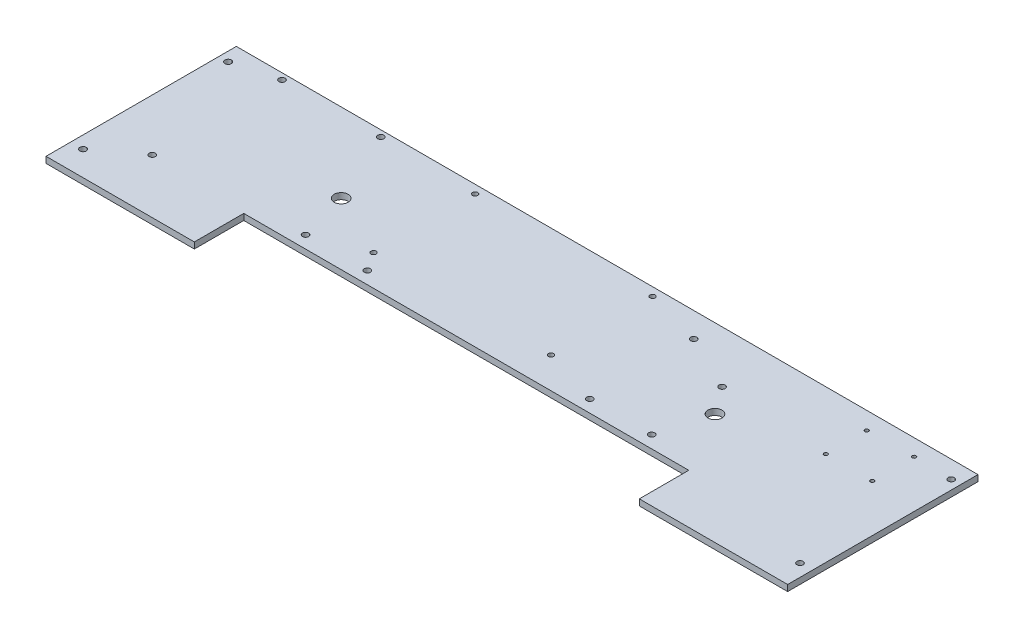
SolidWorks part; units mm, degrees
ref_plane "Front Plane" through (0, 0, 0) normal (0, 0, 1) x (1, 0, 0)
ref_plane "Top Plane" through (0, 0, 0) normal (0, 1, 0) x (1, 0, 0)
ref_plane "Right Plane" through (0, 0, 0) normal (1, 0, 0) x (0, 0, -1)
sketch "Sketch1" plane through (0, 0, 0) normal (0, 1, 0) x (1, 0, 0)
  line L0 (0, 0) -> (457.2, 0)
  line L1 (457.2, 0) -> (457.2, -50.8)
  line L2 (457.2, -50.8) -> (609.6, -50.8)
  line L3 (609.6, -50.8) -> (609.6, 144.78)
  line L4 (609.6, 144.78) -> (-152.4, 144.78)
  line L5 (0, 0) -> (0, -50.8)
  line L6 (0, -50.8) -> (-152.4, -50.8)
  line L7 (-152.4, -50.8) -> (-152.4, 144.78)
  dimension "D1" = 195.58
  dimension "D2" = 195.58
  dimension "D3" = 457.2
  dimension "D4" = 762
  dimension "D5" = 152.4
  dimension "D6" = 152.4
  dimension "D7" = 144.78
extrude "Boss-Extrude1" add sketch "Sketch1" along normal blind 6.35 contours L4 L7 L6 L5 L0 L1 L2 L3
sketch "Sketch3" plane through (0, 6.35, 0) normal (0, 1, 0) x (1, 0, 0)
  line L0 (-152.4, -50.8) -> (-152.4, 144.78) construction
  line L1 (0, -50.8) -> (-152.4, -50.8) construction
  line L3 (609.6, 144.78) -> (-152.4, 144.78) construction
  line L5 (0, 0) -> (457.2, 0) construction
  line L8 (609.6, -50.8) -> (609.6, 144.78) construction
  line L9 (457.2, -50.8) -> (609.6, -50.8) construction
  circle A0 centre (-139.7, -25.4) radius 3.302
  circle A1 centre (-99.1108, 5.0292) radius 3.175
  circle A2 centre (-142.875, 126.8171) radius 3.302
  circle A3 centre (-99.1108, 138.3792) radius 3.175
  circle A4 centre (2.413, 138.3792) radius 3.175
  circle A5 centre (36.576, 63.5) radius 7.1438
  circle A6 centre (600.075, 126.8171) radius 3.175
  circle A7 centre (596.9, -25.4) radius 3.175
  circle A8 centre (560.959, 127.8636) radius 1.905
  circle A9 centre (513.207, 84.8106) radius 1.905
  circle A10 centre (560.959, 84.8106) radius 1.905
  circle A11 centre (513.207, 126.8171) radius 1.905
  circle A12 centre (420.624, 63.5) radius 7.1438
  dimension "D1" = 6.604
  dimension "D2" = 12.7
  dimension "D3" = 25.4
  dimension "D4" = 6.35
  dimension "D5" = 53.2892
  dimension "D6" = 55.8292
  dimension "D7" = 6.604
  dimension "D8" = 9.525
  dimension "D9" = 17.9629
  dimension "D10" = 6.35
  dimension "D11" = 6.4008
  dimension "D12" = 53.2892
  dimension "D13" = 6.35
  dimension "D14" = 154.813
  dimension "D15" = 6.4008
  dimension "D16" = 14.2875
  dimension "D17" = 188.976
  dimension "D18" = 63.5
  dimension "D20" = 6.35
  dimension "D21" = 9.525
  dimension "D22" = 17.9629
  dimension "D23" = 6.35
  dimension "D24" = 12.7
  dimension "D25" = 25.4
  dimension "D26" = 3.81
  dimension "D27" = 48.641
  dimension "D28" = 16.9164
  dimension "D29" = 3.81
  dimension "D30" = 59.9694
  dimension "D31" = 96.393
  dimension "D32" = 3.81
  dimension "D33" = 48.641
  dimension "D34" = 59.9694
  dimension "D35" = 3.81
  dimension "D36" = 17.9629
  dimension "D37" = 96.393
  dimension "D38" = 14.2875
  dimension "D39" = 81.28
  dimension "D40" = 188.976
extrude "Cut-Extrude1" cut sketch "Sketch3" against normal blind 7.62
sketch "Sketch5" plane through (0, 6.35, 0) normal (0, 1, 0) x (1, 0, 0)
  line L0 (609.6, 144.78) -> (-152.4, 144.78) construction
  line L1 (44.45, 144.78) -> (412.75, 144.78)
  line L2 (44.45, 144.78) -> (44.45, 0)
  line L3 (44.45, 0) -> (412.75, 0)
  line L4 (412.75, 144.78) -> (412.75, 0)
  line L5 (0, 0) -> (457.2, 0) construction
  line L8 (-152.4, -50.8) -> (-152.4, 144.78) construction
  line L9 (0, 0) -> (0, -50.8) construction
  circle A0 centre (101.6, 136.144) radius 2.667
  circle A1 centre (36.576, 63.5) radius 7.1438 construction
  circle A2 centre (101.6, 31.75) radius 2.667
  circle A3 centre (420.624, 63.5) radius 7.1438 construction
  circle A4 centre (400.05, 91.44) radius 3.175
  circle A5 centre (406.4, 12.7) radius 3.175
  circle A6 centre (342.9, 119.38) radius 3.175
  circle A7 centre (342.9, 12.7) radius 3.175
  circle A8 centre (283.8704, 136.144) radius 2.667
  circle A9 centre (283.8704, 31.75) radius 2.667
  circle A10 centre (114.3, 12.7) radius 3.175
  circle A11 centre (50.8, 12.7) radius 3.175
  circle A12 centre (2.413, 138.3792) radius 3.175 construction
  dimension "D5" = 7.874
  dimension "D7" = 44.45
  dimension "D1" = 7.874
  dimension "D9" = 6.35
  dimension "D10" = 12.7
  dimension "D11" = 53.34
  dimension "D12" = 6.35
  dimension "D13" = 6.35
  dimension "D14" = 12.7
  dimension "D15" = 6.35
  dimension "D16" = 25.4
  dimension "D17" = 69.85
  dimension "D18" = 6.35
  dimension "D19" = 12.7
  dimension "D20" = 69.85
  dimension "D21" = 5.334
  dimension "D22" = 8.636
  dimension "D23" = 128.8796
  dimension "D24" = 5.334
  dimension "D25" = 128.8796
  dimension "D26" = 113.03
  dimension "D27" = 5.334
  dimension "D28" = 8.636
  dimension "D29" = 311.15
  dimension "D30" = 5.334
  dimension "D31" = 113.03
  dimension "D32" = 311.15
  dimension "D33" = 6.35
  dimension "D34" = 12.7
  dimension "D35" = 298.45
  dimension "D36" = 6.35
  dimension "D37" = 12.7
  dimension "D38" = 6.35
  dimension "D39" = 42.037
  dimension "D2" = 7.874
  dimension "D3" = 196.85
  dimension "D4" = 7.874
  dimension "D6" = 368.3
  dimension "D8" = 144.78
extrude "Cut-Extrude2" cut sketch "Sketch5" against normal blind 7.62 contours A11 | A2 | A10 | A0 | A8 | A6 | A9 | A4 | A7 | A5
